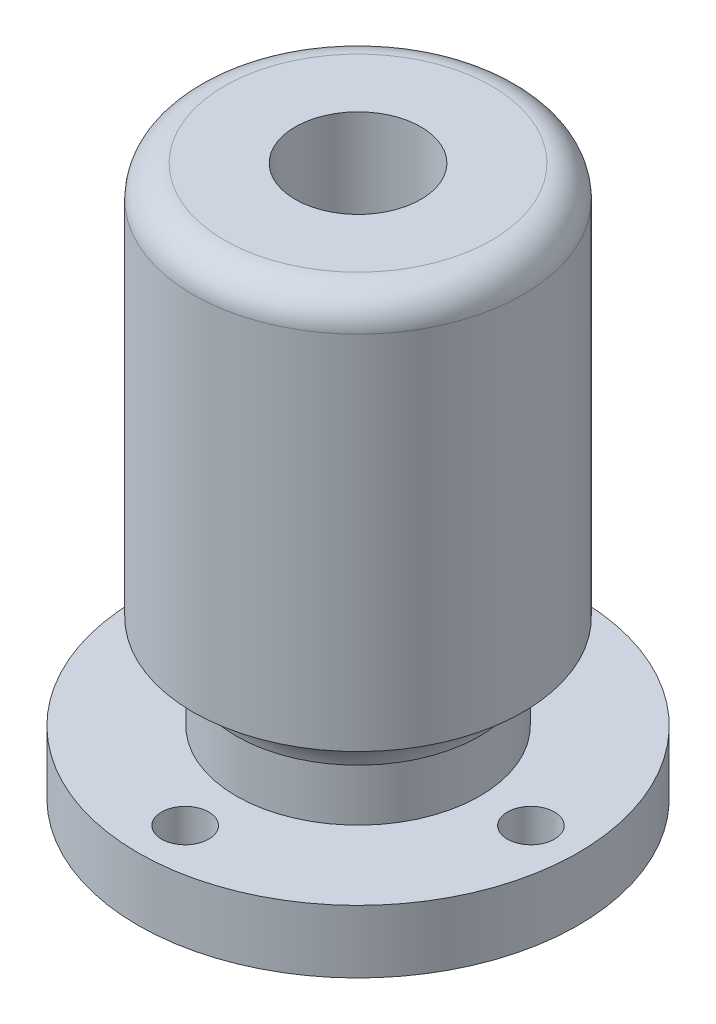
SolidWorks part; units mm, degrees
ref_plane "Front Plane" through (0, 0, 0) normal (0, 0, 1) x (1, 0, 0)
ref_plane "Top Plane" through (0, 0, 0) normal (0, 1, 0) x (1, 0, 0)
ref_plane "Right Plane" through (0, 0, 0) normal (1, 0, 0) x (0, 0, -1)
sketch "Sketch1" plane through (0, 0, 0) normal (0, 1, 0) x (1, 0, 0)
  circle A0 centre (0, 0) radius 14
  circle A1 centre (0, 11) radius 1.5
  circle A2 centre (0, -11) radius 1.5
  circle A3 centre (11, 0) radius 1.5
  circle A4 centre (-11, 0) radius 1.5
  circle A5 centre (0, 0) radius 4.25
  dimension "D1" = 28
  dimension "D2" = 3
  dimension "D3" = 3
  dimension "D4" = 3
  dimension "D5" = 3
  dimension "D6" = 11
  dimension "D7" = 22
  dimension "D8" = 22
  dimension "D9" = 11
extrude "Boss-Extrude1" add sketch "Sketch1" along normal blind 4
sketch "Sketch2" plane through (0, 4, 0) normal (0, 1, 0) x (1, 0, 0)
  circle A0 centre (0, 0) radius 7.75
  circle A1 centre (0, 0) radius 4.25
  dimension "D1" = 15.5
extrude "Boss-Extrude2" add sketch "Sketch2" along normal blind 6
sketch "Sketch3" plane through (0, 10, 0) normal (0, 1, 0) x (1, 0, 0)
  circle A0 centre (0, 0) radius 10.5
  circle A1 centre (0, 0) radius 4
  dimension "D1" = 8
  dimension "D2" = 21
extrude "Boss-Extrude3" add sketch "Sketch3" along normal blind 25 separate body
sketch "Sketch4" plane through (0, 0, 0) normal (1, 0, 0) x (0, 0, -1)
  line L0 (7.75, 10) -> (10.5, 10)
  line L1 (7.75, 10) -> (7.75, 7.3045)
  line L2 (7.75, 4) -> (7.75, 10) construction
  spline S0 degree 2 poles (10.5, 10) (8.2892, 9.5069) (7.75, 7.3045) knots 0 0 0 1 1 1
ref_axis "Axis1" through (0, 36.75, 0) along (0, -1, 0)
revolve "Revolve1" add sketch "Sketch4" angle 360 about axis through (0, 36.75, 0) along (0, -1, 0)
ref_plane "Plane1" through (0, 0, 0) normal (-0.7071, 0, 0.7071) x (0.7071, 0, 0.7071)
fillet "Fillet1" radius 2 1 edges at (0, 35, 10.5)
